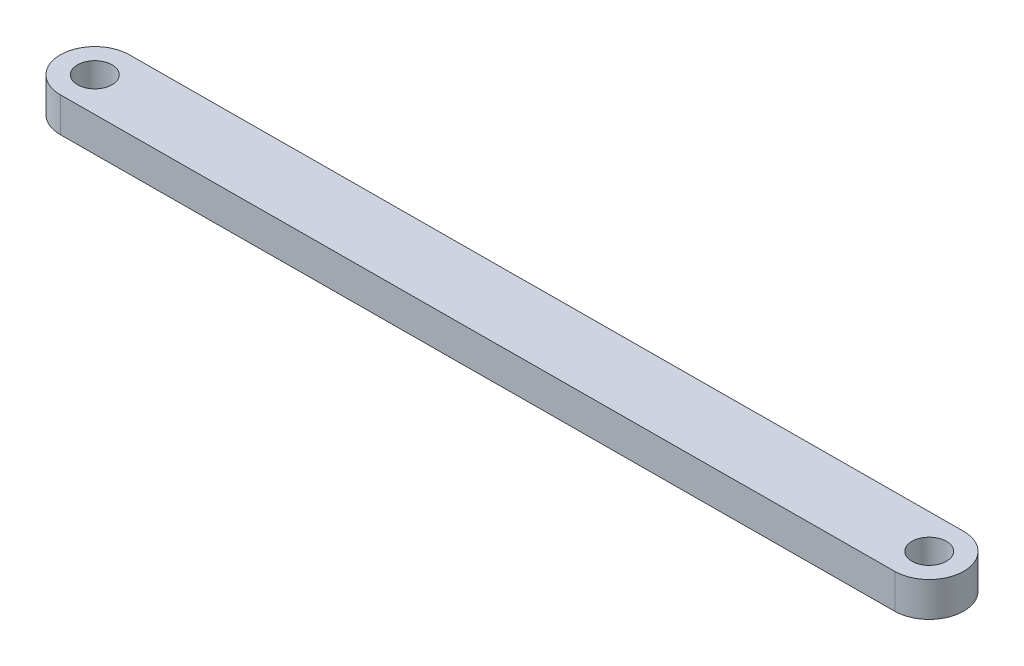
SolidWorks part; units mm, degrees
ref_plane "Front Plane" through (0, 0, 0) normal (0, 0, 1) x (1, 0, 0)
ref_plane "Top Plane" through (0, 0, 0) normal (0, 1, 0) x (1, 0, 0)
ref_plane "Right Plane" through (0, 0, 0) normal (1, 0, 0) x (0, 0, -1)
sketch "Sketch1" plane through (0, 0, 0) normal (0, 1, 0) x (1, 0, 0)
  line L0 (0, 0) -> (304.8, 1.6535) construction
  line L1 (-0.0689, 12.6998) -> (304.7311, 14.3533)
  line L2 (0.0689, -12.6998) -> (304.8689, -11.0464)
  arc A0 (-0.0689, 12.6998) -> (0.0689, -12.6998) centre (0, 0) ccw
  arc A1 (304.8689, -11.0464) -> (304.7311, 14.3533) centre (304.8, 1.6535) ccw
  circle A2 centre (0, 0) radius 6.35
  circle A3 centre (304.8, 1.6535) radius 6.35
  point P3 (152.4, 0.8267)
  dimension "D3" = 12.7
  dimension "D4" = 12.7
  dimension "D1" = 25.4
  dimension "D2" = 304.8
extrude "Boss-Extrude1" add sketch "Sketch1" along normal blind 12.7
